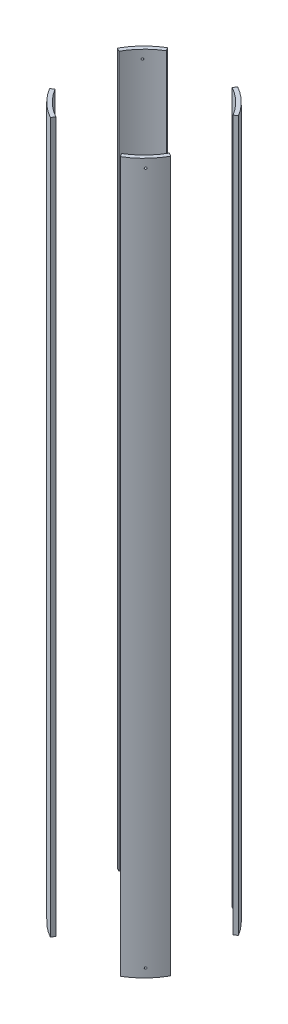
SolidWorks part; units mm, degrees
material "6061-T6 (SS)"
ref_plane "Front Plane" through (0, 0, 0) normal (0, 0, 1) x (1, 0, 0)
ref_plane "Top Plane" through (0, 0, 0) normal (0, 1, 0) x (1, 0, 0)
ref_plane "Right Plane" through (0, 0, 0) normal (1, 0, 0) x (0, 0, -1)
sketch "Sketch2" plane through (0, 0, 0) normal (0, 1, 0) x (1, 0, 0)
  circle A0 centre (0, 0) radius 88.9
  circle A1 centre (0, 0) radius 83.82
  dimension "D1" = 177.8
  dimension "D2" = 167.64
extrude "Boss-Extrude1" add sketch "Sketch2" along normal mid plane 917.2143
sketch "Sketch3" plane through (0, 0, 0) normal (0, 1, 0) x (1, 0, 0)
  line L0 (0, 0) -> (169.6618, 101.6776)
  line L1 (-58.1167, 96.9749) -> (0, 0)
  line L2 (0, 0) -> (53.9, 96.9749)
  line L3 (53.9, 96.9749) -> (-58.1167, 96.9749)
  line L4 (0, 0) -> (70.9917, -118.4586)
  line L5 (70.9917, -118.4586) -> (-65.8409, -118.4586)
  line L6 (-65.8409, -118.4586) -> (0, 0)
  line L7 (169.6618, 101.6776) -> (169.6618, -94.3004)
  line L8 (169.6618, -94.3004) -> (0, 0)
  line L9 (0, 0) -> (-123.7413, 68.7771)
  line L10 (-123.7413, 68.7771) -> (-123.7413, -74.1577)
  line L11 (-123.7413, -74.1577) -> (0, 0)
  dimension "D1" = 60
  dimension "D2" = 60
  dimension "D3" = 60
  dimension "D4" = 60
  dimension "D5" = 30
  dimension "D6" = 30
extrude "Cut-Extrude1" cut sketch "Sketch3" against normal through all both and the other way through all contours L8 L7 L0 | L2 L3 L1 | L10 L11 L9 | L6 L5 L4
ref_plane "Bolt reference plane" through (-56.3092, 0, 58.1758) normal (0.6955, 0, -0.7185) x (-0.7185, 0, -0.6955)
sketch "Sketch5" plane through (-56.3092, 0, 58.1758) normal (0.6955, 0, -0.7185) x (-0.7185, 0, -0.6955)
  line L0 (-23.009, -458.6072) -> (23.009, -458.6072) construction
  circle A0 centre (-0.0228, 447.4947) radius 1.27
  circle A1 centre (-0.0228, -447.4947) radius 1.27
  dimension "D1" = 2.54
  dimension "D4" = 11.1125
  dimension "D2" = 21.717
  dimension "D3" = 11.1125
extrude "Bolt holes" cut sketch "Sketch5" against normal through all
pattern_circular "Bolt pattern" count 4 over 360 about axis through (0, 458.6072, 0) along (0, 1, 0) of "Bolt holes"
equation "\"D1@Boss-Extrude1\"=3*12"
